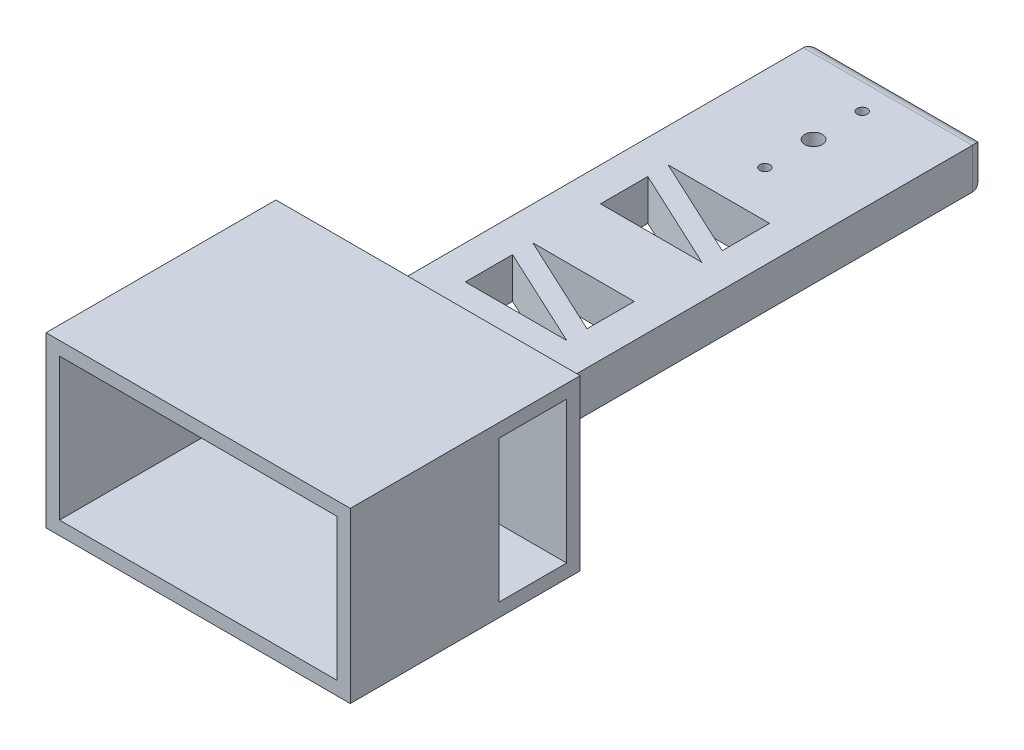
SolidWorks part; units mm, degrees
ref_plane "Front Plane" through (0, 0, 0) normal (0, 0, 1) x (1, 0, 0)
ref_plane "Top Plane" through (0, 0, 0) normal (0, 1, 0) x (1, 0, 0)
ref_plane "Right Plane" through (0, 0, 0) normal (1, 0, 0) x (0, 0, -1)
sketch "Sketch1" plane through (0, 0, 0) normal (0, 0, 1) x (1, 0, 0)
  line L1 (-12.5, -3) -> (12.5, -3)
  line L2 (-12.5, -3) -> (-12.5, 3)
  line L3 (-12.5, 3) -> (12.5, 3)
  line L4 (12.5, -3) -> (12.5, 3)
  line L5 (-12.5, -3) -> (12.5, 3) construction
  line L6 (-12.5, 3) -> (12.5, -3) construction
  point P0 (0, 0)
  dimension "D1" = 25
  dimension "D2" = 6
extrude "Boss-Extrude1" add sketch "Sketch1" along normal blind 70
fillet "Fillet1" radius 2 4 edges at (12.5, 0, 0) (-12.5, 0, 0) (0, 3, 0) (0, -3, 0)
sketch "Sketch2" plane through (0, 3, 0) normal (0, 1, 0) x (1, 0, 0)
  line L0 (12.5, -70) -> (12.5, -2) construction
  line L1 (7.5, -7) -> (-7.5, -7)
  line L2 (7.5, -7) -> (7.5, -65)
  line L3 (7.5, -65) -> (-7.5, -65)
  line L4 (-7.5, -7) -> (-7.5, -65)
  line L5 (-12.5, -70) -> (-12.5, -2) construction
  line L6 (12.5, -2) -> (-12.5, -2) construction
  line L7 (12.5, -70) -> (-12.5, -70) construction
  line L8 (-7.5, -7) -> (7.5, -13.9946)
  line L9 (7.5, -16.9946) -> (-7.5, -10)
  line L10 (7.5, -16.9946) -> (-7.5, -16.9946)
  dimension "D1" = 5
  dimension "D2" = 5
  dimension "D3" = 5
  dimension "D4" = 5
  dimension "D5" = 25
  dimension "D6" = 3
extrude "Cut-Extrude1" cut sketch "Sketch2" against normal up to next (6 mm away) contours L10 L9 L4 | L1 L8 L2
pattern_linear "LPattern1" count 3 spacing 20 along (0, 0, 1) of "Cut-Extrude1"
sketch "Sketch3" plane through (0, 3, 0) normal (0, 1, 0) x (1, 0, 0)
  line L1 (-7.5, -7) -> (7.5, -7)
  line L2 (-7.5, -7) -> (-7.5, -16.9946)
  line L3 (-7.5, -16.9946) -> (7.5, -16.9946)
  line L4 (7.5, -7) -> (7.5, -16.9946)
extrude "Boss-Extrude4" add sketch "Sketch3" against normal up to surface (6 mm away) contours L2 L1 L4 L3 up to face at (2.5, -3, 49.3315)
sketch "Sketch4" plane through (0, 0, 70) normal (0, 0, 1) x (1, 0, 0)
  line L6 (-22.5, -12.5) -> (22.5, -12.5)
  line L10 (-22.5, -12.5) -> (-22.5, 12.5)
  line L11 (-22.5, 12.5) -> (22.5, 12.5)
  line L12 (22.5, -12.5) -> (22.5, 12.5)
  line L13 (-22.5, -12.5) -> (22.5, 12.5) construction
  line L14 (-22.5, 12.5) -> (22.5, -12.5) construction
  point P0 (0, 0)
  point P1 (0, 0)
  dimension "D1" = 45
  dimension "D2" = 25
extrude "Boss-Extrude5" add sketch "Sketch4" along normal blind 2
sketch "Sketch5" plane through (0, 0, 72) normal (0, 0, 1) x (1, 0, 0)
  line L8 (20.5, -10.5) -> (20.5, 10.5)
  line L9 (20.5, 10.5) -> (-20.5, 10.5)
  line L10 (-20.5, 10.5) -> (-20.5, -10.5)
  line L11 (-20.5, -10.5) -> (20.5, -10.5)
  line L12 (20.5, -10.5) -> (20.5, 10.5)
  line L13 (20.5, 10.5) -> (-20.5, 10.5)
  line L14 (-20.5, 10.5) -> (-20.5, -10.5)
  line L15 (-20.5, -10.5) -> (20.5, -10.5)
  line L16 (22.5, -12.5) -> (22.5, 12.5)
  line L17 (22.5, 12.5) -> (-22.5, 12.5)
  line L18 (-22.5, 12.5) -> (-22.5, -12.5)
  line L19 (-22.5, -12.5) -> (22.5, -12.5)
  line L20 (22.5, -12.5) -> (22.5, 12.5)
  line L21 (22.5, 12.5) -> (-22.5, 12.5)
  line L22 (-22.5, 12.5) -> (-22.5, -12.5)
  line L23 (-22.5, -12.5) -> (22.5, -12.5)
  dimension "D1" = 2
  dimension "D2" = 0
extrude "Boss-Extrude6" add sketch "Sketch5" along normal blind 32
fillet "Fillet2" radius 5 4 edges at (0, 3, 70) (-12.5, 0, 70) (12.5, 0, 70) (0, -3, 70)
sketch "Sketch6" plane through (0, 0, 104) normal (0, 0, 1) x (1, 0, 0)
  line L0 (22.5, 12.5) -> (-22.5, 12.5) construction
  line L1 (-28.5, -12.5) -> (28.5, -12.5)
  line L2 (-28.5, -12.5) -> (-28.5, 12.5)
  line L3 (-28.5, 12.5) -> (28.5, 12.5)
  line L4 (28.5, -12.5) -> (28.5, 12.5)
  line L5 (-28.5, -12.5) -> (28.5, 12.5) construction
  line L6 (-28.5, 12.5) -> (28.5, -12.5) construction
  line L7 (0, 27.5306) -> (0, -27.9773) construction
  line L8 (42.5341, 0) -> (-46.7994, 0) construction
  line L9 (20.5, -10.5) -> (20.5, 10.5) construction
  line L10 (22.5, -12.5) -> (22.5, 12.5) construction
  circle A0 centre (24, 5) radius 1.3
  point P0 (0, 0)
  dimension "D1" = 2.6
  dimension "D2" = 3.5
  dimension "D3" = 5
  dimension "D4" = 6
sketch "Sketch8" plane through (22.5, 0, 0) normal (1, 0, 0) x (0, 0, -1)
  line L0 (-104, 12.5) -> (-70, 12.5) construction
  line L1 (-82, 10.5) -> (-72, 10.5)
  line L2 (-82, 10.5) -> (-82, -10.5)
  line L3 (-82, -10.5) -> (-72, -10.5)
  line L4 (-72, 10.5) -> (-72, -10.5)
  line L5 (-104, -12.5) -> (-70, -12.5) construction
  line L7 (-70, -12.5) -> (-70, 12.5) construction
  dimension "D1" = 2
  dimension "D2" = 2
  dimension "D3" = 2
  dimension "D4" = 10
extrude "Cut-Extrude2" cut sketch "Sketch8" against normal up to surface (45 mm away) up to face at (-22.5, 0, 87)
sketch "Sketch9" plane through (0, -3, 0) normal (0, -1, 0) x (1, 0, 0)
  line L0 (-16.0531, 13) -> (16.0819, 13) construction
  circle A0 centre (0, 13) radius 10.5
  circle A1 centre (0, 13) radius 1.3
  circle A2 centre (0, 20.2) radius 0.75
  circle A3 centre (0, 5.8) radius 0.75
  dimension "D2" = 21
  dimension "D3" = 2.6
  dimension "D4" = 1.5
  dimension "D1" = 13
  dimension "D5" = 7.2
extrude "Cut-Extrude3" cut sketch "Sketch9" against normal up to next contours L0 A1 | A1 L0 | A2 | A3
